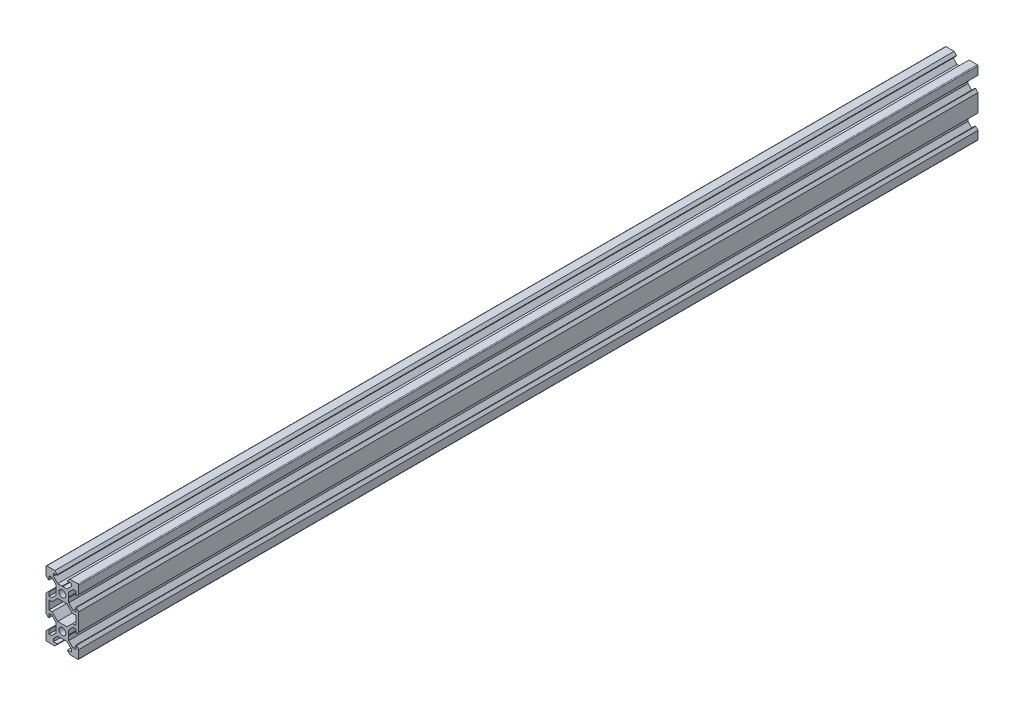
SolidWorks part; units mm, degrees
material "6061-T6 (SS)"
ref_plane "Front Plane" through (0, 0, 0) normal (0, 0, 1) x (1, 0, 0)
ref_plane "Top Plane" through (0, 0, 0) normal (0, 1, 0) x (1, 0, 0)
ref_plane "Right Plane" through (0, 0, 0) normal (1, 0, 0) x (0, 0, -1)
sketch "Sketch1" plane through (0, 0, 0) normal (0, 0, 1) x (1, 0, 0)
  line L0 (0, 0) -> (10, 0) construction
  line L1 (9.5, -20) -> (-9.5, -20)
  line L2 (10, -19.5) -> (10, 19.5)
  line L3 (9.5, 20) -> (-9.5, 20)
  line L4 (-10, -19.5) -> (-10, 19.5)
  line L5 (10, -20) -> (-10, 20) construction
  line L6 (10, 20) -> (-10, -20) construction
  circle A0 centre (0, 10) radius 2.1
  circle A1 centre (0, -10) radius 2.1
  arc A2 (-9.5, -20) -> (-10, -19.5) centre (-9.5, -19.5) cw
  arc A3 (9.5, -20) -> (10, -19.5) centre (9.5, -19.5) ccw
  arc A4 (10, 19.5) -> (9.5, 20) centre (9.5, 19.5) ccw
  arc A5 (-9.5, 20) -> (-10, 19.5) centre (-9.5, 19.5) ccw
  point P0 (0, 0)
  line B0 (0, 10) -> (0, 20) construction
  line B1 (0, 13.69) -> (-0.21, 13.9)
  line B2 (-0.21, 13.9) -> (-2.8393, 13.9)
  line B3 (-2.8393, 13.9) -> (-5.5, 16.5607)
  line B4 (-5.5, 16.5607) -> (-5.5, 18.2)
  line B5 (-5.5, 18.2) -> (-3.125, 18.2)
  line B6 (-3.125, 18.2) -> (-3.125, 18.545)
  line B7 (-3.125, 18.545) -> (-4.58, 20)
  line B8 (-4.58, 20) -> (4.58, 20)
  line B9 (0, 10) -> (-5.9132, 15.9132) construction
  line B10 (3.125, 18.545) -> (4.58, 20)
  line B11 (3.125, 18.2) -> (3.125, 18.545)
  line B12 (5.5, 18.2) -> (3.125, 18.2)
  line B13 (5.5, 16.5607) -> (5.5, 18.2)
  line B14 (2.8393, 13.9) -> (5.5, 16.5607)
  line B15 (0.21, 13.9) -> (2.8393, 13.9)
  line B16 (0, 13.69) -> (0.21, 13.9)
  line B17 (0, 10) -> (-10, 10) construction
  line B18 (-3.69, 10) -> (-3.9, 9.79)
  line B19 (-3.9, 9.79) -> (-3.9, 7.1607)
  line B20 (-3.9, 7.1607) -> (-6.5607, 4.5)
  line B21 (-6.5607, 4.5) -> (-8.2, 4.5)
  line B22 (-8.2, 4.5) -> (-8.2, 6.875)
  line B23 (-8.2, 6.875) -> (-8.545, 6.875)
  line B24 (-8.545, 6.875) -> (-10, 5.42)
  line B25 (-10, 5.42) -> (-10, 14.58)
  line B26 (0, 10) -> (-5.9132, 4.0868) construction
  line B27 (-8.545, 13.125) -> (-10, 14.58)
  line B28 (-8.2, 13.125) -> (-8.545, 13.125)
  line B29 (-8.2, 15.5) -> (-8.2, 13.125)
  line B30 (-6.5607, 15.5) -> (-8.2, 15.5)
  line B31 (-3.9, 12.8393) -> (-6.5607, 15.5)
  line B32 (-3.9, 10.21) -> (-3.9, 12.8393)
  line B33 (-3.69, 10) -> (-3.9, 10.21)
  line B34 (0, -10) -> (-10, -10) construction
  line B35 (-3.69, -10) -> (-3.9, -10.21)
  line B36 (-3.9, -10.21) -> (-3.9, -12.8393)
  line B37 (-3.9, -12.8393) -> (-6.5607, -15.5)
  line B38 (-6.5607, -15.5) -> (-8.2, -15.5)
  line B39 (-8.2, -15.5) -> (-8.2, -13.125)
  line B40 (-8.2, -13.125) -> (-8.545, -13.125)
  line B41 (-8.545, -13.125) -> (-10, -14.58)
  line B42 (-10, -14.58) -> (-10, -5.42)
  line B43 (0, -10) -> (-5.9132, -15.9132) construction
  line B44 (-8.545, -6.875) -> (-10, -5.42)
  line B45 (-8.2, -6.875) -> (-8.545, -6.875)
  line B46 (-8.2, -4.5) -> (-8.2, -6.875)
  line B47 (-6.5607, -4.5) -> (-8.2, -4.5)
  line B48 (-3.9, -7.1607) -> (-6.5607, -4.5)
  line B49 (-3.9, -9.79) -> (-3.9, -7.1607)
  line B50 (-3.69, -10) -> (-3.9, -9.79)
  line B51 (0, -10) -> (0, -20) construction
  line B52 (0, -13.69) -> (0.21, -13.9)
  line B53 (0.21, -13.9) -> (2.8393, -13.9)
  line B54 (2.8393, -13.9) -> (5.5, -16.5607)
  line B55 (5.5, -16.5607) -> (5.5, -18.2)
  line B56 (5.5, -18.2) -> (3.125, -18.2)
  line B57 (3.125, -18.2) -> (3.125, -18.545)
  line B58 (3.125, -18.545) -> (4.58, -20)
  line B59 (4.58, -20) -> (-4.58, -20)
  line B60 (0, -10) -> (5.9132, -15.9132) construction
  line B61 (-3.125, -18.545) -> (-4.58, -20)
  line B62 (-3.125, -18.2) -> (-3.125, -18.545)
  line B63 (-5.5, -18.2) -> (-3.125, -18.2)
  line B64 (-5.5, -16.5607) -> (-5.5, -18.2)
  line B65 (-2.8393, -13.9) -> (-5.5, -16.5607)
  line B66 (-0.21, -13.9) -> (-2.8393, -13.9)
  line B67 (0, -13.69) -> (-0.21, -13.9)
  line B68 (0, -10) -> (10, -10) construction
  line B69 (3.69, -10) -> (3.9, -9.79)
  line B70 (3.9, -9.79) -> (3.9, -7.1607)
  line B71 (3.9, -7.1607) -> (6.5607, -4.5)
  line B72 (6.5607, -4.5) -> (8.2, -4.5)
  line B73 (8.2, -4.5) -> (8.2, -6.875)
  line B74 (8.2, -6.875) -> (8.545, -6.875)
  line B75 (8.545, -6.875) -> (10, -5.42)
  line B76 (10, -5.42) -> (10, -14.58)
  line B77 (0, -10) -> (5.9132, -4.0868) construction
  line B78 (8.545, -13.125) -> (10, -14.58)
  line B79 (8.2, -13.125) -> (8.545, -13.125)
  line B80 (8.2, -15.5) -> (8.2, -13.125)
  line B81 (6.5607, -15.5) -> (8.2, -15.5)
  line B82 (3.9, -12.8393) -> (6.5607, -15.5)
  line B83 (3.9, -10.21) -> (3.9, -12.8393)
  line B84 (3.69, -10) -> (3.9, -10.21)
  line B85 (0, 10) -> (10, 10) construction
  line B86 (3.69, 10) -> (3.9, 10.21)
  line B87 (3.9, 10.21) -> (3.9, 12.8393)
  line B88 (3.9, 12.8393) -> (6.5607, 15.5)
  line B89 (6.5607, 15.5) -> (8.2, 15.5)
  line B90 (8.2, 15.5) -> (8.2, 13.125)
  line B91 (8.2, 13.125) -> (8.545, 13.125)
  line B92 (8.545, 13.125) -> (10, 14.58)
  line B93 (10, 14.58) -> (10, 5.42)
  line B94 (0, 10) -> (5.9132, 15.9132) construction
  line B95 (8.545, 6.875) -> (10, 5.42)
  line B96 (8.2, 6.875) -> (8.545, 6.875)
  line B97 (8.2, 4.5) -> (8.2, 6.875)
  line B98 (6.5607, 4.5) -> (8.2, 4.5)
  line B99 (3.9, 7.1607) -> (6.5607, 4.5)
  line B100 (3.9, 9.79) -> (3.9, 7.1607)
  line B101 (3.69, 10) -> (3.9, 9.79)
  line B102 (-8.2, -2.7) -> (-8.2, 2.7)
  line B103 (-8.2, 2.7) -> (-6.2393, 2.7)
  line B104 (-6.2393, 2.7) -> (-2.8393, 6.1)
  line B105 (-2.8393, 6.1) -> (2.8393, 6.1)
  line B106 (0, 6.1) -> (0, 0) construction
  line B107 (0, 0) -> (-8.2, 0) construction
  line B108 (6.2393, 2.7) -> (2.8393, 6.1)
  line B109 (8.2, 2.7) -> (6.2393, 2.7)
  line B110 (8.2, -2.7) -> (8.2, 2.7)
  line B111 (8.2, -2.7) -> (6.2393, -2.7)
  line B112 (6.2393, -2.7) -> (2.8393, -6.1)
  line B113 (-2.8393, -6.1) -> (2.8393, -6.1)
  line B114 (-6.2393, -2.7) -> (-2.8393, -6.1)
  line B115 (-8.2, -2.7) -> (-6.2393, -2.7)
  line B116 (0, 6.1) -> (0, 10) construction
  line B117 (0, 10) -> (-5.0927, 4.9073) construction
  dimension "D4" = 4.2
  dimension "D5" = 0.5
  dimension "D1" = 20
  dimension "D2" = 40
  dimension "D3" = 20
sketch_block_instance "V Slot 1-4"
sketch_block "V Slot 1" parameters "D1"=10, "D2"=11, "D3"=4.3, "D4"=1.8, "D5"=0.21, "D6"=45, "D7"=9.16, "D8"=1.5, "D9"=6.25
sketch_block_instance "V Slot 1-5"
sketch_block_instance "V Slot 1-6"
sketch_block_instance "V Slot 1-7"
sketch_block_instance "V Slot 1-8"
sketch_block_instance "V Slot 1-9"
sketch_block_instance "Center Cutout 1-1"
sketch_block "Center Cutout 1" parameters "D1"=5.4, "D2"=12.2, "D3"=8.2, "D4"=45, "D5"=10, "D6"=1.5
extrude "Boss-Extrude1" add sketch "Sketch1" along normal blind 550 contours B101 B86 B87 B88 B89 B90 B91 B92 L2 A4 L3 B10 B11 B12 B13 B14 B15 B16 B1 B2 B3 B4 B5 B6 B7 A5 L4 B27 B28 B29 B30 B31 B32 B33 B18 B19 B20 B21 B22 B23 B24 B44 B45 B46 B47 B48 B49 B50 B35
